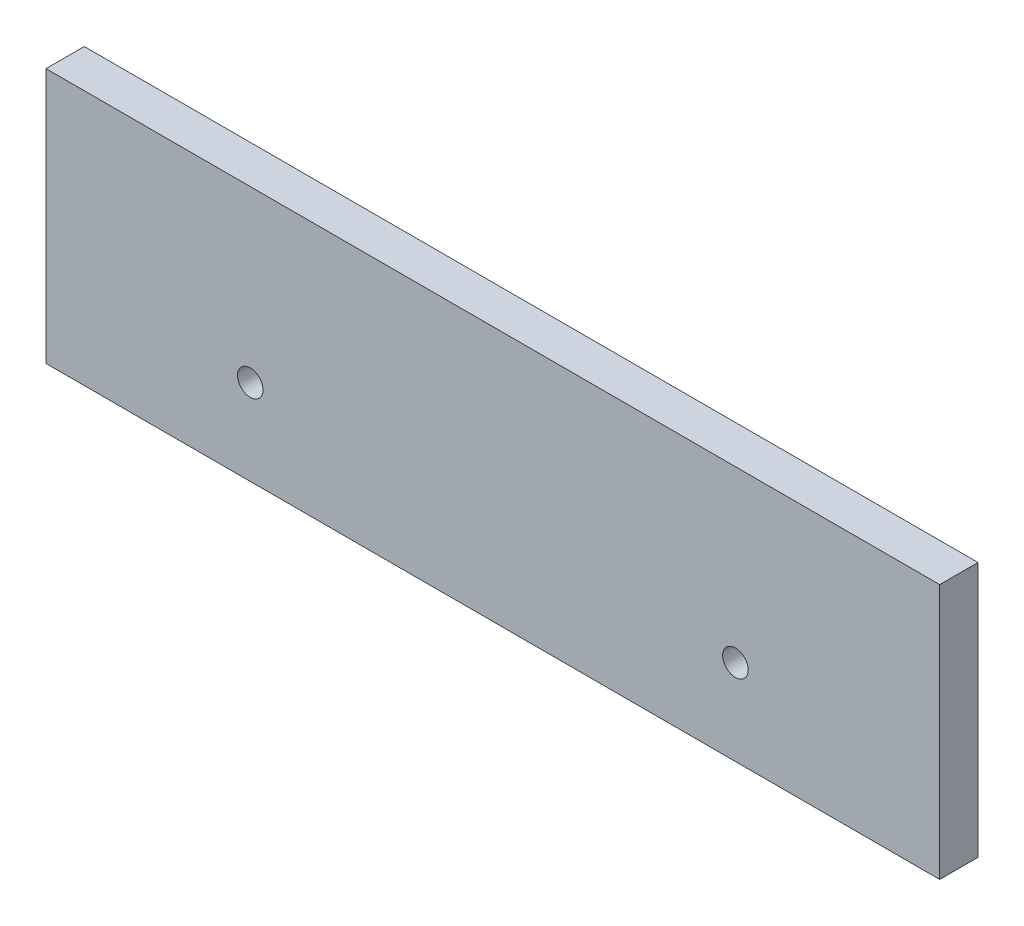
SolidWorks part; units mm, degrees
material "Balsa"
ref_plane "Front Plane" through (0, 0, 0) normal (0, 0, 1) x (1, 0, 0)
ref_plane "Top Plane" through (0, 0, 0) normal (0, 1, 0) x (1, 0, 0)
ref_plane "Right Plane" through (0, 0, 0) normal (1, 0, 0) x (0, 0, -1)
sketch "Sketch2" plane through (0, 0, 24.3119) normal (0, 0, -1) x (-1, 0, 0)
  line L0 (121.1498, 12.2405) -> (471.1498, 12.2405)
  line L1 (121.1498, 12.2405) -> (121.1498, 112.2405)
  line L2 (121.1498, 112.2405) -> (471.1498, 112.2405)
  line L3 (471.1498, 12.2405) -> (471.1498, 112.2405)
  circle A0 centre (201.1498, 45.7405) radius 5
  circle A1 centre (391.1498, 45.7405) radius 5
  dimension "D1" = 350
  dimension "D2" = 100
extrude "Boss-Extrude1" add sketch "Sketch2" against normal blind 15
